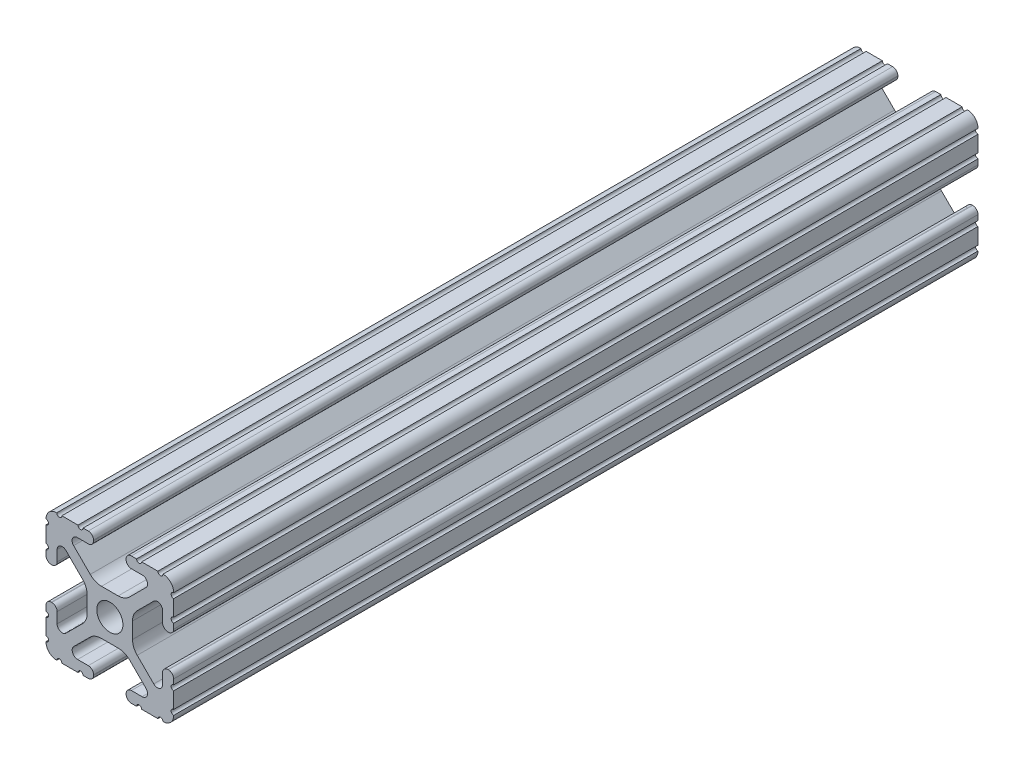
SolidWorks part; units mm, degrees
ref_plane "Front Plane" through (0, 0, 0) normal (0, 0, 1) x (1, 0, 0)
ref_plane "Top Plane" through (0, 0, 0) normal (0, 1, 0) x (1, 0, 0)
ref_plane "Right Plane" through (0, 0, 0) normal (1, 0, 0) x (0, 0, -1)
sketch "Sketch1" plane through (0, 0, 0) normal (0, 0, 1) x (1, 0, 0)
  line L88 (-7.1797, -8.6452) -> (-3.9523, -5.4237)
  line L89 (-1.7093, -4.4958) -> (1.7093, -4.4958)
  line L90 (3.9523, -5.4237) -> (7.1797, -8.6452)
  line L91 (6.4164, -10.4902) -> (4.2875, -10.4902)
  line L92 (3.2385, -11.5392) -> (3.2385, -11.651)
  line L93 (4.2875, -12.7) -> (5.3171, -12.7)
  line L94 (6.3331, -12.7) -> (9.5504, -12.7)
  line L95 (12.7, -9.5504) -> (12.7, -6.3331)
  line L96 (12.7, -5.3171) -> (12.7, -4.2875)
  line L97 (11.651, -3.2385) -> (11.5392, -3.2385)
  line L98 (10.4902, -4.2875) -> (10.4902, -6.4021)
  line L99 (8.7371, -7.1294) -> (5.441, -3.8408)
  line L100 (4.5085, -1.5932) -> (4.5085, 1.5932)
  line L101 (5.441, 3.8408) -> (8.7371, 7.1294)
  line L102 (10.4902, 6.4021) -> (10.4902, 4.2875)
  line L103 (11.5392, 3.2385) -> (11.651, 3.2385)
  line L104 (12.7, 4.2875) -> (12.7, 5.3171)
  line L105 (12.7, 6.3331) -> (12.7, 9.5504)
  line L106 (9.5504, 12.7) -> (6.3331, 12.7)
  line L107 (5.3171, 12.7) -> (4.2875, 12.7)
  line L108 (3.2385, 11.651) -> (3.2385, 11.5392)
  line L109 (4.2875, 10.4902) -> (6.4768, 10.4902)
  line L110 (7.207, 8.7244) -> (3.8983, 5.4232)
  line L111 (1.6558, 4.4958) -> (-1.6558, 4.4958)
  line L112 (-3.8983, 5.4232) -> (-7.207, 8.7244)
  line L113 (-6.4768, 10.4902) -> (-4.2875, 10.4902)
  line L114 (-3.2385, 11.5392) -> (-3.2385, 11.651)
  line L115 (-4.2875, 12.7) -> (-5.3171, 12.7)
  line L116 (-6.3331, 12.7) -> (-9.5504, 12.7)
  line L117 (-12.7, 9.5504) -> (-12.7, 6.3331)
  line L118 (-12.7, 5.3171) -> (-12.7, 4.2875)
  line L119 (-11.651, 3.2385) -> (-11.5392, 3.2385)
  line L120 (-10.4902, 4.2875) -> (-10.4902, 6.4021)
  line L121 (-8.7371, 7.1294) -> (-5.441, 3.8408)
  line L122 (-4.5085, 1.5932) -> (-4.5085, -1.5932)
  line L123 (-5.441, -3.8408) -> (-8.7371, -7.1294)
  line L124 (-10.4902, -6.4021) -> (-10.4902, -4.2875)
  line L125 (-11.5392, -3.2385) -> (-11.651, -3.2385)
  line L126 (-12.7, -4.2875) -> (-12.7, -5.3171)
  line L127 (-12.7, -6.3331) -> (-12.7, -9.5504)
  line L128 (-9.5504, -12.7) -> (-6.3331, -12.7)
  line L129 (-5.3171, -12.7) -> (-4.2875, -12.7)
  line L130 (-3.2385, -11.651) -> (-3.2385, -11.5392)
  line L131 (-4.2875, -10.4902) -> (-6.4164, -10.4902)
  circle A1 centre (0, 0) radius 2.6035
  arc A104 (-7.1797, -8.6452) -> (-6.4164, -10.4902) centre (-6.4164, -9.4098) ccw
  arc A105 (-1.7093, -4.4958) -> (-3.9523, -5.4237) centre (-1.7093, -7.6708) ccw
  arc A106 (3.9523, -5.4237) -> (1.7093, -4.4958) centre (1.7093, -7.6708) ccw
  arc A107 (6.4164, -10.4902) -> (7.1797, -8.6452) centre (6.4164, -9.4098) ccw
  arc A108 (4.2875, -10.4902) -> (3.2385, -11.5392) centre (4.2875, -11.5392) ccw
  arc A109 (3.2385, -11.651) -> (4.2875, -12.7) centre (4.2875, -11.651) ccw
  arc A110 (6.3331, -12.7) -> (5.3171, -12.7) centre (5.8251, -12.7) ccw
  arc A111 (10.5664, -12.6998) -> (9.5504, -12.7) centre (10.0584, -12.7) ccw
  arc A112 (10.5664, -12.6998) -> (12.6998, -10.5664) centre (10.5918, -10.5918) ccw
  arc A113 (12.7, -9.5504) -> (12.6998, -10.5664) centre (12.7, -10.0584) ccw
  arc A114 (12.7, -5.3171) -> (12.7, -6.3331) centre (12.7, -5.8251) ccw
  arc A115 (12.7, -4.2875) -> (11.651, -3.2385) centre (11.651, -4.2875) ccw
  arc A116 (11.5392, -3.2385) -> (10.4902, -4.2875) centre (11.5392, -4.2875) ccw
  arc A117 (8.7371, -7.1294) -> (10.4902, -6.4021) centre (9.4628, -6.4021) ccw
  arc A118 (4.5085, -1.5932) -> (5.441, -3.8408) centre (7.6835, -1.5932) ccw
  arc A119 (5.441, 3.8408) -> (4.5085, 1.5932) centre (7.6835, 1.5932) ccw
  arc A120 (10.4902, 6.4021) -> (8.7371, 7.1294) centre (9.4628, 6.4021) ccw
  arc A121 (10.4902, 4.2875) -> (11.5392, 3.2385) centre (11.5392, 4.2875) ccw
  arc A122 (11.651, 3.2385) -> (12.7, 4.2875) centre (11.651, 4.2875) ccw
  arc A123 (12.7, 6.3331) -> (12.7, 5.3171) centre (12.7, 5.8251) ccw
  arc A124 (12.6998, 10.5664) -> (12.7, 9.5504) centre (12.7, 10.0584) ccw
  arc A125 (12.6998, 10.5664) -> (10.5664, 12.6998) centre (10.5918, 10.5918) ccw
  arc A126 (9.5504, 12.7) -> (10.5664, 12.6998) centre (10.0584, 12.7) ccw
  arc A127 (5.3171, 12.7) -> (6.3331, 12.7) centre (5.8251, 12.7) ccw
  arc A128 (4.2875, 12.7) -> (3.2385, 11.651) centre (4.2875, 11.651) ccw
  arc A129 (3.2385, 11.5392) -> (4.2875, 10.4902) centre (4.2875, 11.5392) ccw
  arc A130 (7.207, 8.7244) -> (6.4768, 10.4902) centre (6.4768, 9.4563) ccw
  arc A131 (1.6558, 4.4958) -> (3.8983, 5.4232) centre (1.6558, 7.6708) ccw
  arc A132 (-3.8983, 5.4232) -> (-1.6558, 4.4958) centre (-1.6558, 7.6708) ccw
  arc A133 (-6.4768, 10.4902) -> (-7.207, 8.7244) centre (-6.4768, 9.4563) ccw
  arc A134 (-4.2875, 10.4902) -> (-3.2385, 11.5392) centre (-4.2875, 11.5392) ccw
  arc A135 (-3.2385, 11.651) -> (-4.2875, 12.7) centre (-4.2875, 11.651) ccw
  arc A136 (-6.3331, 12.7) -> (-5.3171, 12.7) centre (-5.8251, 12.7) ccw
  arc A137 (-10.5664, 12.6998) -> (-9.5504, 12.7) centre (-10.0584, 12.7) ccw
  arc A138 (-10.5664, 12.6998) -> (-12.6998, 10.5664) centre (-10.5918, 10.5918) ccw
  arc A139 (-12.7, 9.5504) -> (-12.6998, 10.5664) centre (-12.7, 10.0584) ccw
  arc A140 (-12.7, 5.3171) -> (-12.7, 6.3331) centre (-12.7, 5.8251) ccw
  arc A141 (-12.7, 4.2875) -> (-11.651, 3.2385) centre (-11.651, 4.2875) ccw
  arc A142 (-11.5392, 3.2385) -> (-10.4902, 4.2875) centre (-11.5392, 4.2875) ccw
  arc A143 (-8.7371, 7.1294) -> (-10.4902, 6.4021) centre (-9.4628, 6.4021) ccw
  arc A144 (-4.5085, 1.5932) -> (-5.441, 3.8408) centre (-7.6835, 1.5932) ccw
  arc A145 (-5.441, -3.8408) -> (-4.5085, -1.5932) centre (-7.6835, -1.5932) ccw
  arc A146 (-10.4902, -6.4021) -> (-8.7371, -7.1294) centre (-9.4628, -6.4021) ccw
  arc A147 (-10.4902, -4.2875) -> (-11.5392, -3.2385) centre (-11.5392, -4.2875) ccw
  arc A148 (-11.651, -3.2385) -> (-12.7, -4.2875) centre (-11.651, -4.2875) ccw
  arc A149 (-12.7, -6.3331) -> (-12.7, -5.3171) centre (-12.7, -5.8251) ccw
  arc A150 (-12.6998, -10.5664) -> (-12.7, -9.5504) centre (-12.7, -10.0584) ccw
  arc A151 (-12.6998, -10.5664) -> (-10.5664, -12.6998) centre (-10.5918, -10.5918) ccw
  arc A152 (-9.5504, -12.7) -> (-10.5664, -12.6998) centre (-10.0584, -12.7) ccw
  arc A153 (-5.3171, -12.7) -> (-6.3331, -12.7) centre (-5.8251, -12.7) ccw
  arc A154 (-4.2875, -12.7) -> (-3.2385, -11.651) centre (-4.2875, -11.651) ccw
  arc A155 (-3.2385, -11.5392) -> (-4.2875, -10.4902) centre (-4.2875, -11.5392) ccw
extrude "Boss-Extrude1" add sketch "Sketch1" along normal mid plane 160
